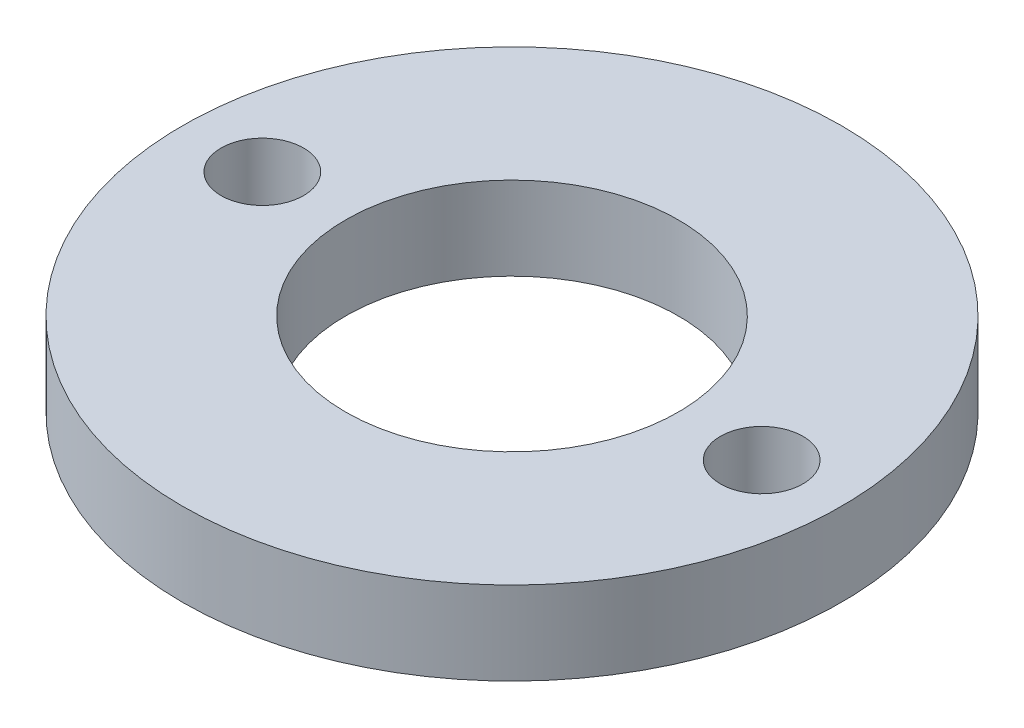
SolidWorks part; units mm, degrees
ref_plane "Front Plane" through (0, 0, 0) normal (0, 0, 1) x (1, 0, 0)
ref_plane "Top Plane" through (0, 0, 0) normal (0, 1, 0) x (1, 0, 0)
ref_plane "Right Plane" through (0, 0, 0) normal (1, 0, 0) x (0, 0, -1)
sketch "Sketch1" plane through (0, 0, 0) normal (0, 1, 0) x (1, 0, 0)
  circle A0 centre (0, 0) radius 12.573
  circle A1 centre (0, 0) radius 6.35
  dimension "D1" = 25.146
  dimension "D2" = 12.7
extrude "Boss-Extrude1" add sketch "Sketch1" along normal blind 3.175
sketch "Sketch2" plane through (0, 3.175, 0) normal (0, 1, 0) x (1, 0, 0)
  circle A0 centre (9.525, 0) radius 1.575
  circle A1 centre (-9.525, 0) radius 1.575
  dimension "D1" = 3.15
  dimension "D2" = 19.05
  dimension "D3" = 9.525
extrude "Cut-Extrude1" cut sketch "Sketch2" against normal through all
